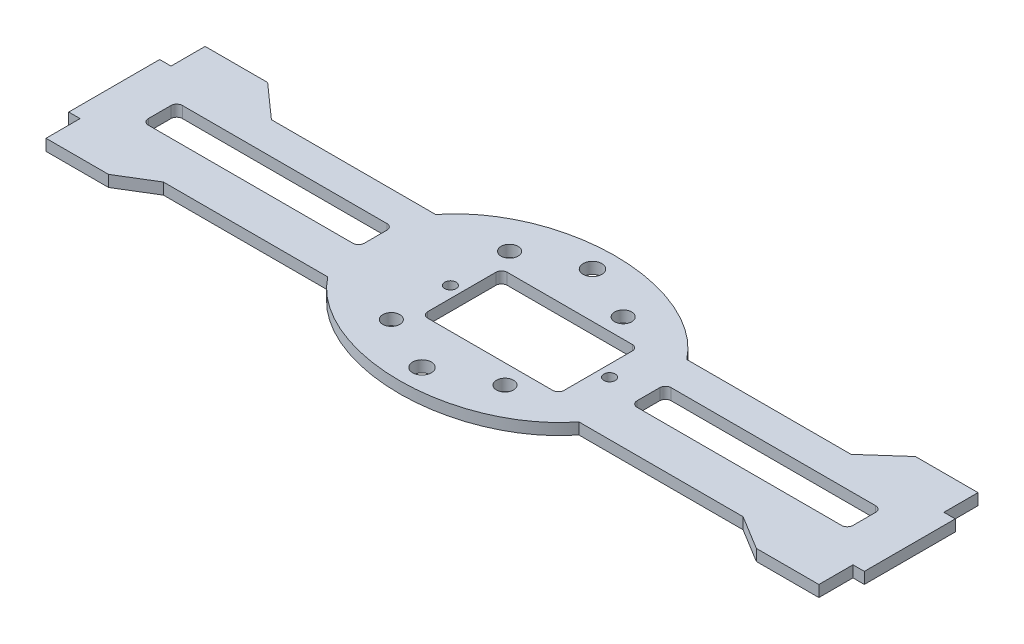
SolidWorks part; units mm, degrees
material "Fibra de Vidro S"
ref_plane "Plano frontal" through (0, 0, 0) normal (0, 0, 1) x (1, 0, 0)
ref_plane "Plano superior" through (0, 0, 0) normal (0, 1, 0) x (1, 0, 0)
ref_plane "Plano direito" through (0, 0, 0) normal (1, 0, 0) x (0, 0, -1)
sketch "Esboço1" plane through (0, 0, 0) normal (0, 1, 0) x (1, 0, 0)
  line L0 (-57, 14.8362) -> (-51, 9.5)
  line L1 (-68, -13.1638) -> (-57, -13.1638)
  line L2 (-68, 14.8362) -> (-68, 8.8362)
  line L3 (-68, 14.8362) -> (-57, 14.8362)
  line L4 (68, -13.1638) -> (68, -7.1638)
  line L5 (-22.0836, 9.5) -> (-51, 9.5)
  line L6 (-22.0836, -9.5) -> (-51, -9.5)
  line L7 (51, 9.5) -> (22.0836, 9.5)
  line L8 (-68, -7.1638) -> (-68, -13.1638)
  line L9 (51, -9.5) -> (22.0836, -9.5)
  line L10 (-68, -7.1638) -> (-70, -7.1638)
  line L11 (57, 14.8362) -> (68, 14.8362)
  line L12 (57, -13.1638) -> (68, -13.1638)
  line L13 (-57, -13.1638) -> (-51, -9.5)
  line L14 (57, 14.8362) -> (51, 9.5)
  line L15 (57, -13.1638) -> (51, -9.5)
  line L16 (68, 8.8362) -> (68, 14.8362)
  line L18 (-68, 8.8362) -> (-70, 8.8362)
  line L19 (-70, -7.1638) -> (-70, 8.8362)
  line L23 (68, -7.1638) -> (70, -7.1638)
  line L25 (68, 8.8362) -> (70, 8.8362)
  line L26 (70, -7.1638) -> (70, 8.8362)
  ellipse E0 centre (0, 0) end of major axis (25.5, 0) minor radius 19 (-22.0836, -9.5) -> (22.0836, -9.5) ccw
  ellipse E1 centre (0, 0) end of major axis (25.5, 0) minor radius 19 (22.0836, 9.5) -> (-22.0836, 9.5) ccw
  point P0 (0, 0)
  point P6 (0, 0)
  point P7 (-68, 0)
  dimension "D1" = 136
  dimension "D2" = 28
  dimension "D3" = 19
  dimension "D4" = 11
  dimension "D5" = 6
  dimension "D6" = 11
  dimension "D7" = 6
  dimension "D8" = 38
  dimension "D9" = 51
  dimension "D10" = 2
  dimension "D11" = 16
  dimension "D12" = 2
  dimension "D13" = 16
extrude "Ressalto-extrusão1" add sketch "Esboço1" along normal blind 2
sketch "Esboço2" plane through (0, 2, 0) normal (0, 1, 0) x (1, 0, 0)
  line L0 (70, -7.1638) -> (70, 8.8362) construction
  line L1 (25, 3.8362) -> (61, 3.8362)
  line L2 (24, 2.8362) -> (24, -1.1638)
  line L3 (25, -2.1638) -> (61, -2.1638)
  line L4 (62, 2.8362) -> (62, -1.1638)
  line L5 (-61, 3.8362) -> (-25, 3.8362)
  line L6 (-62, 2.8362) -> (-62, -1.1638)
  line L7 (-61, -2.1638) -> (-25, -2.1638)
  line L8 (-24, 2.8362) -> (-24, -1.1638)
  line L9 (-70, 8.8362) -> (-70, -7.1638) construction
  line L11 (-7, 7) -> (15, 7)
  line L12 (-8, 6) -> (-8, -6)
  line L13 (-7, -7) -> (15, -7)
  line L14 (16, 6) -> (16, -6)
  line L15 (-8, 7) -> (16, -7) construction
  line L16 (-8, -7) -> (16, 7) construction
  arc A0 (61, 3.8362) -> (62, 2.8362) centre (61, 2.8362) cw
  arc A1 (62, -1.1638) -> (61, -2.1638) centre (61, -1.1638) cw
  arc A2 (25, -2.1638) -> (24, -1.1638) centre (25, -1.1638) cw
  arc A3 (24, 2.8362) -> (25, 3.8362) centre (25, 2.8362) cw
  arc A4 (-25, 3.8362) -> (-24, 2.8362) centre (-25, 2.8362) cw
  arc A5 (-24, -1.1638) -> (-25, -2.1638) centre (-25, -1.1638) cw
  arc A6 (-61, -2.1638) -> (-62, -1.1638) centre (-61, -1.1638) cw
  arc A7 (-62, 2.8362) -> (-61, 3.8362) centre (-61, 2.8362) cw
  arc A8 (16, 6) -> (15, 7) centre (15, 6) ccw
  arc A9 (15, -7) -> (16, -6) centre (15, -6) ccw
  arc A10 (-7, -7) -> (-8, -6) centre (-7, -6) cw
  arc A11 (-8, 6) -> (-7, 7) centre (-7, 6) cw
  circle A12 centre (0, 15) radius 1.65
  circle A13 centre (10, 10.4) radius 1.5
  circle A14 centre (-10, 10.4) radius 1.5
  circle A15 centre (0, -15) radius 1.65
  circle A16 centre (10, -10.4) radius 1.5
  circle A17 centre (-10, -10.4) radius 1.5
  circle A18 centre (-10, 0) radius 1
  circle A19 centre (18, 0) radius 1
  ellipse E0 centre (0, 0) end of major axis (25.5, 0) minor radius 19 (-22.0836, -9.5) -> (22.0836, -9.5) ccw construction
  ellipse E1 centre (0, 0) end of major axis (25.5, 0) minor radius 19 (22.0836, 9.5) -> (-22.0836, 9.5) ccw construction
  point P0 (44.5, -0.4312)
  point P2 (-41.5, -0.4312)
  point P30 (4, 0)
  point P35 (0, -19)
  point P57 (0, 19)
  point P75 (0, -19)
  point P80 (62, 0.8362)
  point P81 (70, 0.8362)
  point P82 (16, 0)
  point P83 (-24, 0.8362)
  dimension "D4" = 1
  dimension "D11" = 1
  dimension "D14" = 3.3
  dimension "D15" = 3
  dimension "D21" = 2
  dimension "D1" = 2
  dimension "D2" = 8
  dimension "D3" = 6
  dimension "D5" = 8
  dimension "D6" = 36
  dimension "D7" = 24
  dimension "D8" = 14
  dimension "D9" = 8
  dimension "D10" = 12
  dimension "D12" = 4
  dimension "D13" = 3.4
  dimension "D16" = 10
  dimension "D17" = 10
  dimension "D18" = 3.4
  dimension "D19" = 3.4
  dimension "D20" = 4
  dimension "D22" = 2
  dimension "D23" = 2
extrude "Corte-extrusão1" cut sketch "Esboço2" against normal through all
